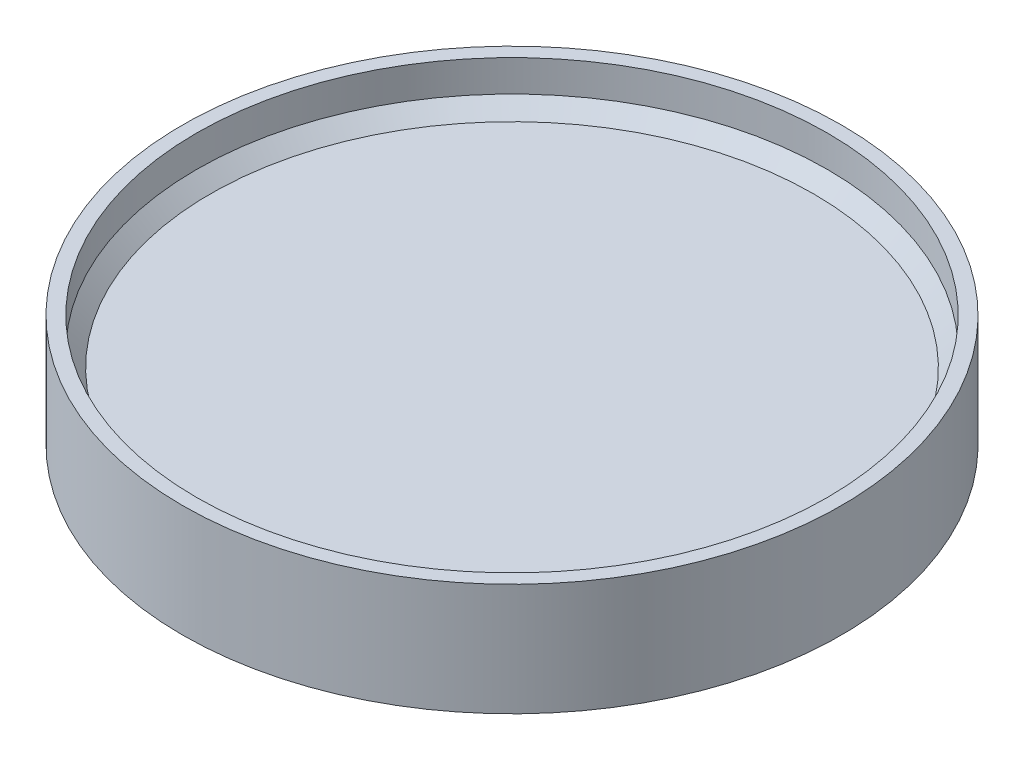
SolidWorks part; units mm, degrees
material "6061-T6 (SS)"
ref_plane "Front Plane" through (0, 0, 0) normal (0, 0, 1) x (1, 0, 0)
ref_plane "Top Plane" through (0, 0, 0) normal (0, 1, 0) x (1, 0, 0)
ref_plane "Right Plane" through (0, 0, 0) normal (1, 0, 0) x (0, 0, -1)
sketch "Sketch5" plane through (0, 0, 0) normal (0, 0, 1) x (1, 0, 0)
  line L0 (0, 9.525) -> (142.875, 9.525)
  line L1 (142.875, 9.525) -> (142.875, 30.1625)
  line L2 (142.875, 30.1625) -> (149.225, 30.1625)
  line L3 (149.225, 30.1625) -> (149.225, -20.6375)
  line L4 (149.225, -20.6375) -> (142.875, -20.6375)
  line L5 (142.875, -20.6375) -> (142.875, 0)
  line L6 (142.875, 0) -> (0, 0)
  line L7 (0, 0) -> (0, 9.525)
  dimension "D1" = 50.8
  dimension "D2" = 9.525
  dimension "D3" = 6.35
  dimension "D4" = 149.225
  dimension "D5" = 20.6375
revolve "Revolve1" add sketch "Sketch5" angle 360 about L7
chamfer "Chamfer1" distance 6.35 angle 45 2 edges at (0, 0, -142.875) (0, 9.525, -142.875)
equation "\"D5@Sketch5\"=(\"D1@Sketch5\"-\"D2@Sketch5\")/2"
